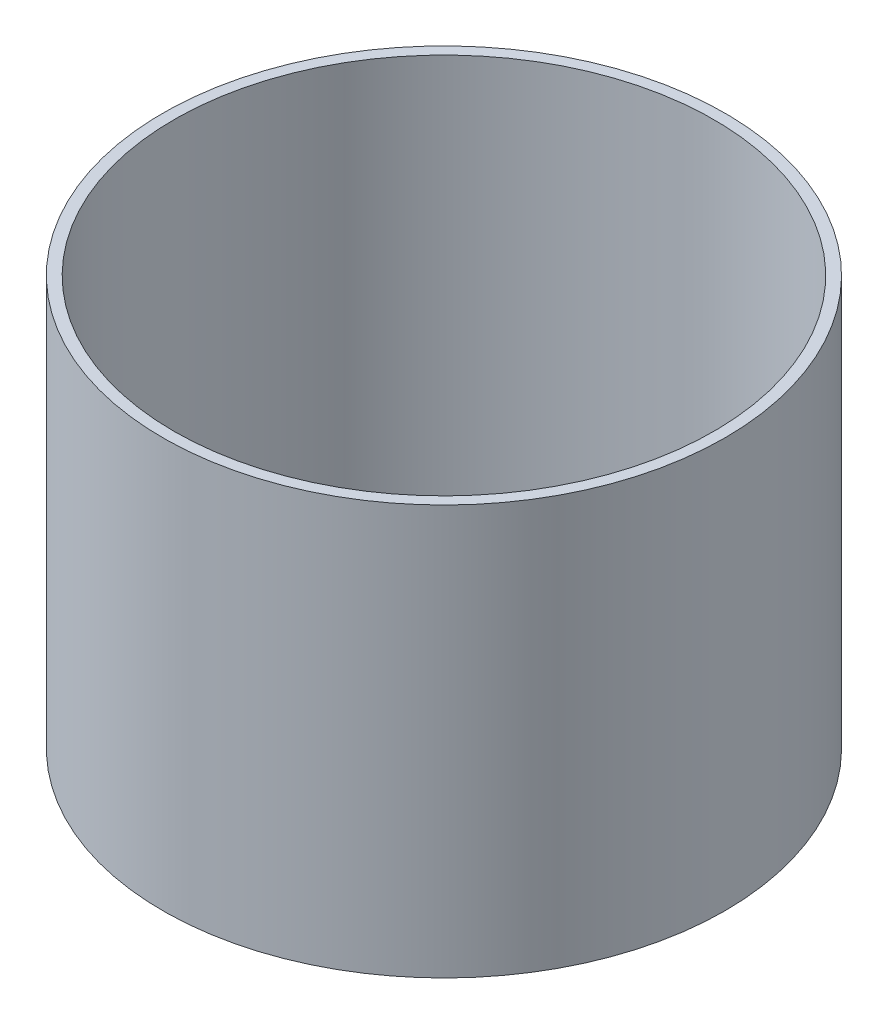
SolidWorks part; units mm, degrees
ref_plane "Front Plane" through (0, 0, 0) normal (0, 0, 1) x (1, 0, 0)
ref_plane "Top Plane" through (0, 0, 0) normal (0, 1, 0) x (1, 0, 0)
ref_plane "Right Plane" through (0, 0, 0) normal (1, 0, 0) x (0, 0, -1)
sketch "Sketch1" plane through (0, 0, 0) normal (0, 1, 0) x (1, 0, 0)
  circle A0 centre (0, 0) radius 184.15
  dimension "D1" = 368.3
extrude "Extrude-Thin1" add sketch "Sketch1" along normal blind 279.4 thin
